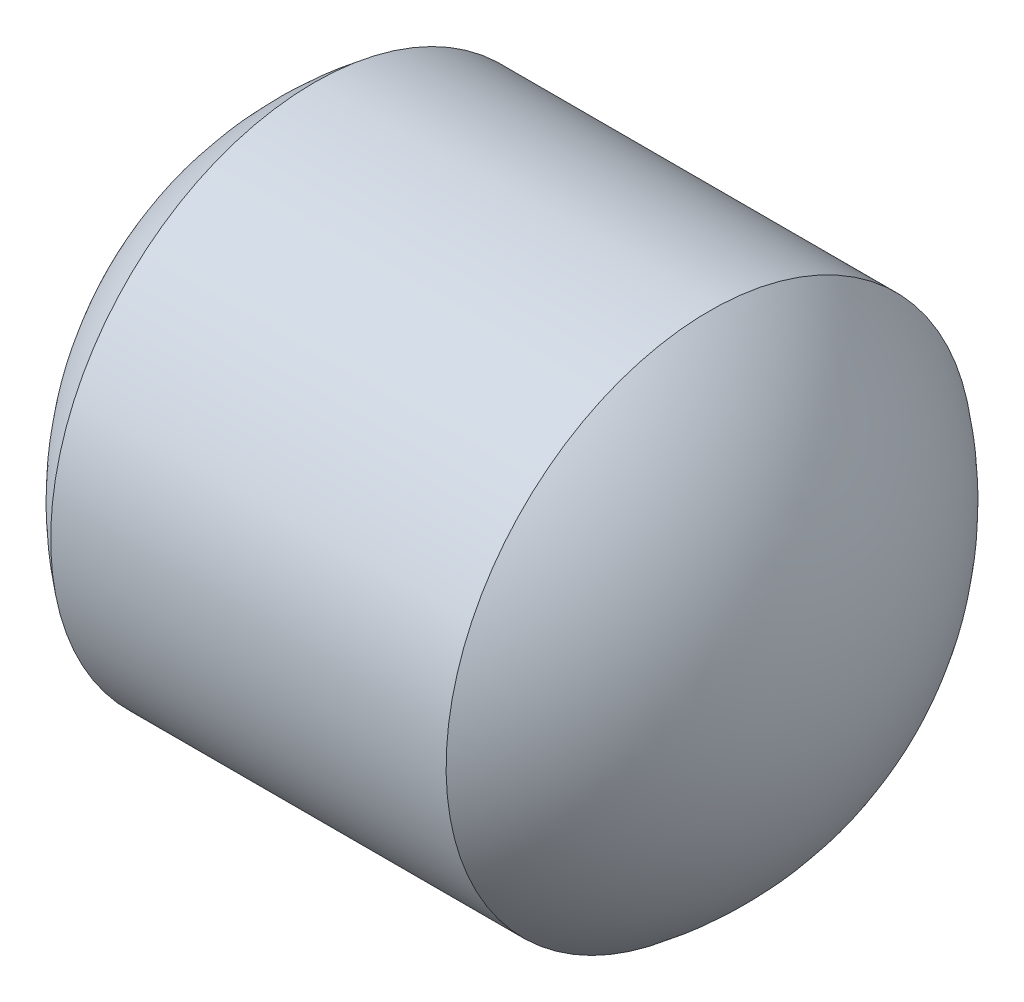
SolidWorks part; units mm, degrees
ref_plane "前视基准面" through (0, 0, 0) normal (0, 0, 1) x (1, 0, 0)
ref_plane "上视基准面" through (0, 0, 0) normal (0, 1, 0) x (1, 0, 0)
ref_plane "右视基准面" through (0, 0, 0) normal (1, 0, 0) x (0, 0, -1)
sketch "草图1" plane through (0, 0, 0) normal (0, 0, 1) x (1, 0, 0)
  line L0 (-0.75, 1) -> (0.75, 1)
  line L1 (-0.75, -1) -> (0.75, -1)
  line L2 (-1.6196, 0) -> (2.0213, 0) construction
  arc A0 (0.75, -1) -> (0.75, 1) centre (0, 0) ccw
  arc A1 (-0.75, 1) -> (-0.75, -1) centre (0, 0) ccw
  dimension "D1" = 2.5
  dimension "D2" = 1
  dimension "D3" = 1
revolve "旋转1" add sketch "草图1" angle 360 about L2
